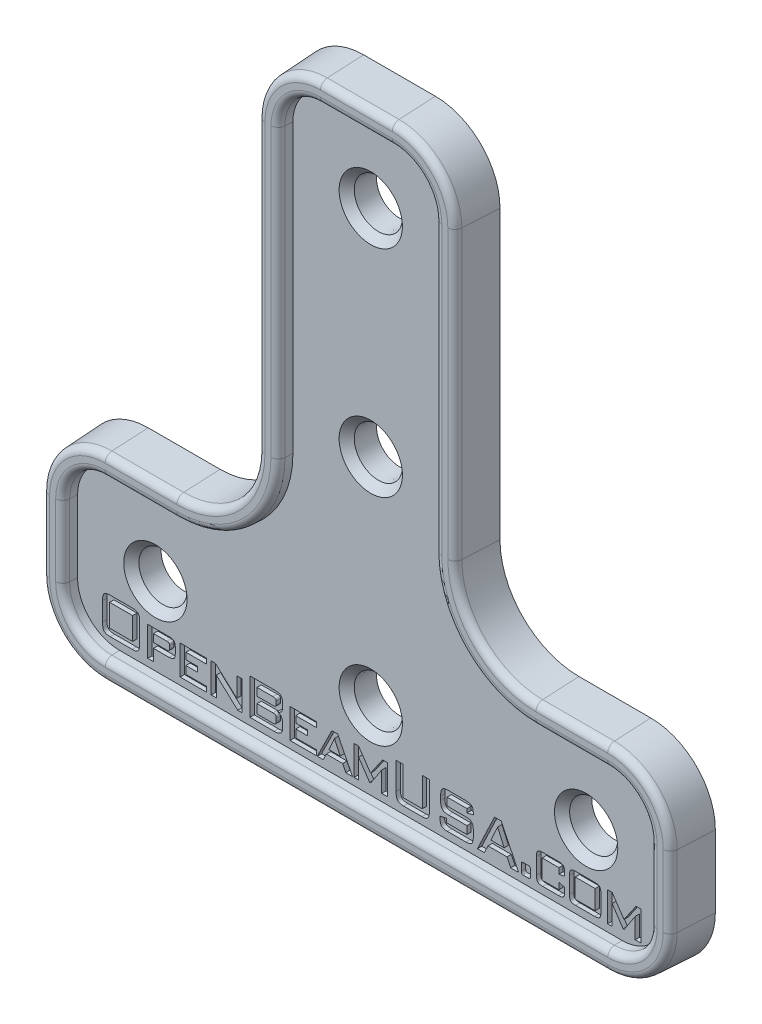
SolidWorks part; units mm, degrees
ref_plane "Front Plane" through (0, 0, 0) normal (0, 0, 1) x (1, 0, 0)
ref_plane "Top Plane" through (0, 0, 0) normal (0, 1, 0) x (1, 0, 0)
ref_plane "Right Plane" through (0, 0, 0) normal (1, 0, 0) x (0, 0, -1)
sketch "Sketch1" plane through (0, 0, 0) normal (0, 0, 1) x (1, 0, 0)
  line L0 (55, 0) -> (-55, 0) construction
  line L1 (-7.5, 30) -> (7.5, 30)
  line L2 (-7.5, 30) -> (-7.5, 0)
  line L3 (7.5, 0) -> (22.5, 0)
  line L4 (7.5, 30) -> (7.5, 0)
  line L5 (-22.5, 0) -> (-7.5, 0)
  line L6 (-22.5, 0) -> (-22.5, -15)
  line L7 (-22.5, -15) -> (22.5, -15)
  line L8 (22.5, 0) -> (22.5, -15)
  line L9 (0, 49.321) -> (0, -31.3726) construction
  line L10 (0, -54.6431) -> (0, 54.6431) construction
  dimension "D1" = 15
  dimension "D2" = 45
  dimension "D3" = 45
extrude "Boss-Extrude1" add sketch "Sketch1" along normal blind 2
fillet "Fillet1" radius 5 8 edges at (22.5, -15, 1) (22.5, 0, 1) (-7.5, 0, 1) (7.5, 0, 1) (7.5, 30, 1) (-22.5, -15, 1) (-22.5, 0, 1) (-7.5, 30, 1)
sketch "Sketch2" plane through (0, 0, 2) normal (0, 0, 1) x (1, 0, 0)
  line L0 (-22.5, -7.5) -> (22.5, -7.5) construction
  line L1 (-22.5, -5) -> (-22.5, -10) construction
  line L2 (22.5, -10) -> (22.5, -5) construction
  line L3 (0, 30) -> (0, -15) construction
  line L4 (2.5, 30) -> (-2.5, 30) construction
  line L5 (-17.5, -15) -> (17.5, -15) construction
  circle A0 centre (-15, -7.5) radius 1.6
  circle A1 centre (0, -7.5) radius 1.6
  circle A2 centre (15, -7.5) radius 1.6
  circle A3 centre (0, 22.5) radius 1.6
  circle A4 centre (0, 7.5) radius 1.6
  dimension "D1" = 3.2
  dimension "D2" = 15
  dimension "D3" = 15
  dimension "D4" = 15
  dimension "D5" = 15
extrude "Cut-Extrude1" cut sketch "Sketch2" against normal through all
other "Move Face1" face at (-9.4822, 1.9822, 1) face at (-15, 0, 1) face at (-20.5178, -1.9822, 1) face at (-22.5, -7.5, 1) face at (-20.5178, -13.0178, 1) face at (0, -15, 1) face at (20.5178, -13.0178, 1) face at (22.5, -7.5, 1) face at (20.5178, -1.9822, 1) face at (15, 0, 1) face at (9.4822, 1.9822, 1) face at (7.5, 15, 1) face at (5.5178, 28.0178, 1) face at (0, 30, 1) face at (-5.5178, 28.0178, 1) face at (-7.5, 15, 1) parameters "D1"=0.5
draft "Draft1" type of draft neutral plane draft angle 3 faces to draft 21 face at (16.6, -7.5, 0) face at (1.6, 22.5, 0) face at (1.6, 7.5, 0) face at (1.6, -7.5, 0) face at (-13.4, -7.5, 0) face at (-20.216, -2.284, 1) face at (-22, -7.5, 1) face at (-20.216, -12.716, 1) face at (0, -14.5, 1) face at (20.216, -12.716, 1) face at (22, -7.5, 1) face at (20.216, -2.284, 1) face at (15, -0.5, 1) face at (9.1805, 1.6805, 1) face at (7, 15, 1) face at (5.216, 27.716, 1) face at (0, 29.5, 1) face at (-5.216, 27.716, 1) face at (-7, 15, 1) face at (-9.1805, 1.6805, 1) face at (-15, -0.5, 1) neutral plane through (0, 0, 0) neutral plane normal (0, 0, -1) reverse direction yes parameters "D1"=3
sketch "Sketch4" plane through (0, 0, 2) normal (0, 0, 1) x (1, 0, 0)
  line L0 (-17.5, -12.9214) -> (17.5, -12.9214)
  line L1 (20.4214, -10) -> (20.4214, -5)
  line L2 (17.5, -2.0786) -> (12.5, -2.0786)
  line L3 (5.4214, 5) -> (5.4214, 25)
  line L4 (2.5, 27.9214) -> (-2.5, 27.9214)
  line L5 (-5.4214, 25) -> (-5.4214, 5)
  line L6 (-12.5, -2.0786) -> (-17.5, -2.0786)
  line L7 (-20.4214, -5) -> (-20.4214, -10)
  line L8 (-17.5, -14.3952) -> (17.5, -14.3952)
  line L9 (21.8952, -10) -> (21.8952, -5)
  line L10 (17.5, -0.6048) -> (12.5, -0.6048)
  line L11 (6.8952, 5) -> (6.8952, 25)
  line L12 (2.5, 29.3952) -> (-2.5, 29.3952)
  line L13 (-6.8952, 25) -> (-6.8952, 5)
  line L14 (-12.5, -0.6048) -> (-17.5, -0.6048)
  line L15 (-21.8952, -5) -> (-21.8952, -10)
  line L16 (-17.5, -14.3952) -> (17.5, -14.3952)
  line L17 (21.8952, -10) -> (21.8952, -5)
  line L18 (17.5, -0.6048) -> (12.5, -0.6048)
  line L19 (6.8952, 5) -> (6.8952, 25)
  line L20 (2.5, 29.3952) -> (-2.5, 29.3952)
  line L21 (-6.8952, 25) -> (-6.8952, 5)
  line L22 (-12.5, -0.6048) -> (-17.5, -0.6048)
  line L23 (-21.8952, -5) -> (-21.8952, -10)
  arc A2 (17.5, -12.9214) -> (20.4214, -10) centre (17.5, -10) ccw
  arc A3 (20.4214, -5) -> (17.5, -2.0786) centre (17.5, -5) ccw
  arc A4 (5.4214, 5) -> (12.5, -2.0786) centre (12.5, 5) ccw
  arc A5 (5.4214, 25) -> (2.5, 27.9214) centre (2.5, 25) ccw
  arc A6 (-2.5, 27.9214) -> (-5.4214, 25) centre (-2.5, 25) ccw
  arc A7 (-12.5, -2.0786) -> (-5.4214, 5) centre (-12.5, 5) ccw
  arc A8 (-17.5, -2.0786) -> (-20.4214, -5) centre (-17.5, -5) ccw
  arc A9 (-20.4214, -10) -> (-17.5, -12.9214) centre (-17.5, -10) ccw
  arc A10 (17.5, -14.3952) -> (21.8952, -10) centre (17.5, -10) ccw
  arc A11 (21.8952, -5) -> (17.5, -0.6048) centre (17.5, -5) ccw
  arc A12 (6.8952, 5) -> (12.5, -0.6048) centre (12.5, 5) ccw
  arc A13 (6.8952, 25) -> (2.5, 29.3952) centre (2.5, 25) ccw
  arc A14 (-2.5, 29.3952) -> (-6.8952, 25) centre (-2.5, 25) ccw
  arc A15 (-12.5, -0.6048) -> (-6.8952, 5) centre (-12.5, 5) ccw
  arc A16 (-17.5, -0.6048) -> (-21.8952, -5) centre (-17.5, -5) ccw
  arc A17 (-21.8952, -10) -> (-17.5, -14.3952) centre (-17.5, -10) ccw
  arc A18 (17.5, -14.3952) -> (21.8952, -10) centre (17.5, -10) ccw
  arc A19 (21.8952, -5) -> (17.5, -0.6048) centre (17.5, -5) ccw
  arc A20 (6.8952, 5) -> (12.5, -0.6048) centre (12.5, 5) ccw
  arc A21 (6.8952, 25) -> (2.5, 29.3952) centre (2.5, 25) ccw
  arc A22 (-2.5, 29.3952) -> (-6.8952, 25) centre (-2.5, 25) ccw
  arc A23 (-12.5, -0.6048) -> (-6.8952, 5) centre (-12.5, 5) ccw
  arc A24 (-17.5, -0.6048) -> (-21.8952, -5) centre (-17.5, -5) ccw
  arc A25 (-21.8952, -10) -> (-17.5, -14.3952) centre (-17.5, -10) ccw
  dimension "D1" = 0
extrude "Boss-Extrude3" add sketch "Sketch4" along normal blind 1 draft 3
fillet "Fillet3" radius 0.5 32 edges at (-7.5317, 0.0317, 3) (-5.4738, 15, 3) (-4.6028, 27.1028, 3) (0, 27.9738, 3) (4.6028, 27.1028, 3) (5.4738, 15, 3) (7.5317, 0.0317, 3) (15, -2.0262, 3) (19.6028, -2.8972, 3) (20.4738, -7.5, 3) (19.6028, -12.1028, 3) (0, -12.9738, 3) (-19.6028, -12.1028, 3) (-20.4738, -7.5, 3) (-19.6028, -2.8972, 3) (-8.4997, 0.9997, 3) (-6.8428, 15, 3) (-5.5708, 28.0708, 3) (0, 29.3428, 3) (5.5708, 28.0708, 3) (6.8428, 15, 3) (8.4997, 0.9997, 3) (15, -0.6572, 3) (20.5708, -1.9292, 3) (21.8428, -7.5, 3) (20.5708, -13.0708, 3) (0, -14.3428, 3) (-20.5708, -13.0708, 3) (-21.8428, -7.5, 3) (-20.5708, -1.9292, 3) (-15, -2.0262, 3) (-15, -0.6572, 3)
sketch "Sketch5" plane through (0, 0, 0) normal (0, 0, -1) x (-1, 0, 0)
  line L0 (0, 54.6431) -> (0, -54.6431) construction
  line L1 (-14.5, -13.8) -> (14.5, -13.8)
  line L2 (-15, -13.3) -> (-15, -10.3)
  line L3 (-14.5, -9.8) -> (14.5, -9.8)
  line L4 (15, -13.3) -> (15, -10.3)
  line L5 (-15, -13.8) -> (15, -9.8) construction
  line L6 (-15, -9.8) -> (15, -13.8) construction
  line L7 (17.5, -14.5) -> (-17.5, -14.5) construction
  arc A0 (14.5, -13.8) -> (15, -13.3) centre (14.5, -13.3) ccw
  arc A1 (14.5, -9.8) -> (15, -10.3) centre (14.5, -10.3) cw
  arc A2 (-14.5, -13.8) -> (-15, -13.3) centre (-14.5, -13.3) cw
  arc A3 (-15, -10.3) -> (-14.5, -9.8) centre (-14.5, -10.3) cw
  point P0 (0, -11.8)
  dimension "D4" = 0.5
  dimension "D1" = 30
  dimension "D2" = 4
  dimension "D3" = 0.7
extrude "Cut-Extrude2" cut sketch "Sketch5" against normal blind 0.2 draft 3
sketch "Sketch6" plane through (0, 0, 2) normal (0, 0, 1) x (1, 0, 0)
  line L0 (-19.1832, -12.4214) -> (19.1832, -12.4214) construction
  line L3 (-17.5, -12.9214) -> (17.5, -12.9214) construction
  arc A0 (17.5, -12.949) -> (20.449, -10) centre (17.5, -10) ccw construction
  arc A1 (-20.449, -10) -> (-17.5, -12.949) centre (-17.5, -10) ccw construction
  text T0 "OpenBeamUSA.com" font "BankGothic Md BT" height 2.5
  dimension "D1" = 0.5
extrude "Cut-Extrude3" cut sketch "Sketch6" against normal blind 0.3
sketch "Sketch7" plane through (0, 0, 0) normal (0, 0, -1) x (-1, 0, 0)
  line L0 (-14.9895, -11.8) -> (14.9895, -11.8) construction
  line L2 (14.9895, -13.3) -> (14.9895, -10.3) construction
  text T0 "TL625-000101-001-A \r\n" font "Arial Narrow" height 1.5
  text T1 ">>PA66 + 33GF <<" font "Arial Narrow" height 1
split line "Split Line1"
chamfer "Chamfer1" distance 0.5 angle 45 5 edges at (1.7048, 22.5, 2) (1.7048, 7.5, 2) (-13.2952, -7.5, 2) (1.7048, -7.5, 2) (16.7048, -7.5, 2)
